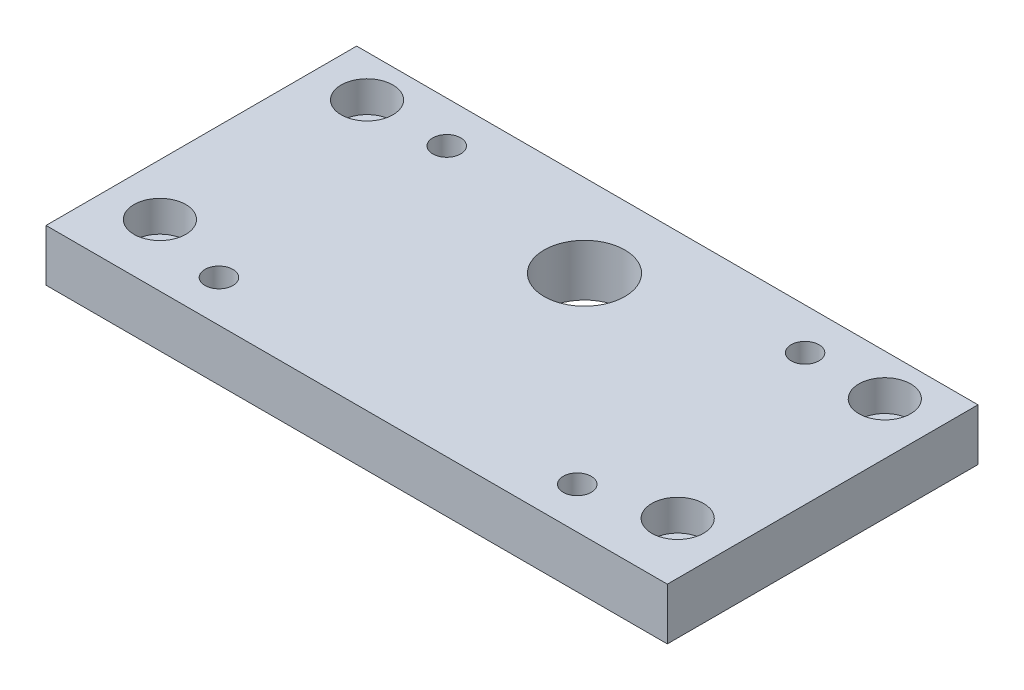
SolidWorks part; units mm, degrees
ref_plane "Front Plane" through (0, 0, 0) normal (0, 0, 1) x (1, 0, 0)
ref_plane "Top Plane" through (0, 0, 0) normal (0, 1, 0) x (1, 0, 0)
ref_plane "Right Plane" through (0, 0, 0) normal (1, 0, 0) x (0, 0, -1)
sketch "Sketch1" plane through (0, 0, 0) normal (0, 1, 0) x (1, 0, 0)
  line L1 (0, 0) -> (60, 0)
  line L2 (0, 0) -> (0, 30)
  line L3 (0, 30) -> (60, 30)
  line L4 (60, 0) -> (60, 30)
  dimension "D1" = 30
  dimension "D2" = 60
extrude "Boss-Extrude1" add sketch "Sketch1" along normal blind 5
sketch "Sketch3" plane through (0, 5, 0) normal (0, 1, 0) x (1, 0, 0)
  line L0 (60, 0) -> (60, 30) construction
  line L1 (60, 30) -> (0, 30) construction
  circle A0 centre (30, 22) radius 3.9
  circle A1 centre (47.3, 4) radius 1.35
  circle A2 centre (47.3, 26) radius 1.35
  dimension "D1" = 30
  dimension "D2" = 8
  dimension "D3" = 7.8
  dimension "D4" = 17.3
  dimension "D5" = 18
  dimension "D6" = 2.7
  dimension "D7" = 2.7
  dimension "D8" = 4
  dimension "D9" = 0
extrude "Cut-Extrude1" cut sketch "Sketch3" against normal blind 5
ref_plane "Plane1" through (30, 0, 0) normal (-1, 0, 0) x (0, 0, 1)
mirror "Mirror1" about plane through (30, 0, 0) normal (-1, 0, 0) of "Cut-Extrude1"
sketch "Sketch4" plane through (0, 5, 0) normal (0, 1, 0) x (1, 0, 0)
  circle A0 centre (55, 26) radius 1.25
  circle A1 centre (30, 22) radius 3.9 construction
  circle A2 centre (55, 6) radius 1.25
  circle A3 centre (30, 22) radius 3.9 construction
  dimension "D1" = 2.5
  dimension "D2" = 25
  dimension "D3" = 2.5
  dimension "D4" = 4
  dimension "D5" = 16
extrude "Cut-Extrude2" cut sketch "Sketch4" against normal blind 5
mirror "Mirror2" about plane through (30, 0, 0) normal (-1, 0, 0) of "Cut-Extrude2"
sketch "Sketch5" plane through (0, 5, 0) normal (0, 1, 0) x (1, 0, 0)
  circle A0 centre (55, 26) radius 2.5
  circle A1 centre (55, 6) radius 2.5
  dimension "D1" = 5
  dimension "D2" = 5
extrude "Cut-Extrude3" cut sketch "Sketch5" against normal blind 3
mirror "Mirror3" about plane through (30, 0, 0) normal (-1, 0, 0) of "Cut-Extrude3"
